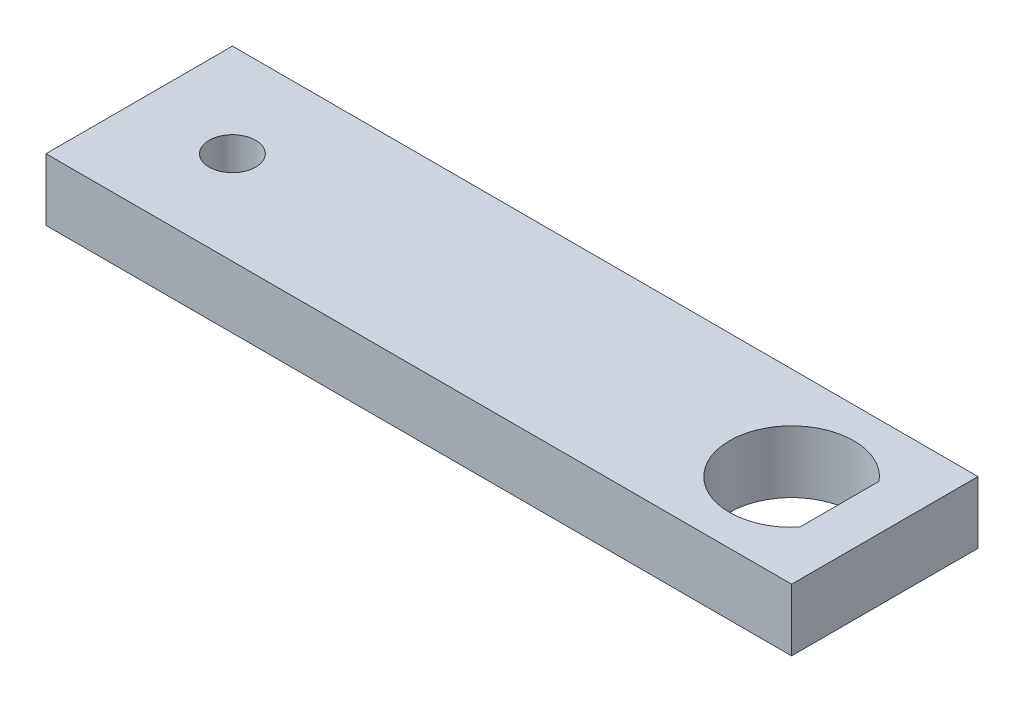
SolidWorks part; units mm, degrees
ref_plane "Front" through (0, 0, 0) normal (0, 0, 1) x (1, 0, 0)
ref_plane "Top" through (0, 0, 0) normal (0, 1, 0) x (-1, 0, 0)
ref_plane "Right" through (0, 0, 0) normal (1, 0, 0) x (0, 0, -1)
sketch "Sketch1" plane through (0, 0, 0) normal (0, 0, 1) x (1, 0, 0)
  line L0 (0, 0) -> (76.2, 0)
  line L1 (0, 0) -> (0, 6.35)
  line L2 (76.2, 6.35) -> (0, 6.35)
  line L3 (76.2, 6.35) -> (76.2, 0)
  dimension "D1" = 6.35
  dimension "D2" = 76.2
extrude "Base-Extrude" add sketch "Sketch1" along normal blind 19.05
sketch "Sketch2" plane through (0, 6.35, 0) normal (0, 1, 0) x (-1, 0, 0)
  line L0 (-76.2, 19.05) -> (-76.2, 0) construction
  line L1 (-76.2, 19.05) -> (0, 19.05) construction
  line L2 (-71.5645, 5.4734) -> (-71.5645, 13.5766)
  arc A0 (-71.5645, 5.4734) -> (-71.5645, 13.5766) centre (-66.675, 9.525) ccw
  dimension "D1" = 12.7
  dimension "D2" = 9.525
  dimension "D3" = 9.525
  dimension "D4" = 4.8895
extrude "Cut-Extrude1" cut sketch "Sketch2" against normal through all
sketch "Sketch3" plane through (0, 6.35, 0) normal (0, 1, 0) x (-1, 0, 0)
  line L0 (0, 19.05) -> (0, 0) construction
  circle A0 centre (-9.525, 9.525) radius 2.3813
  arc A1 (-71.5645, 5.4734) -> (-71.5645, 13.5766) centre (-66.675, 9.525) ccw construction
  point P5 (-66.675, 9.525)
  dimension "D1" = 4.7625
  dimension "D2" = 9.525
extrude "Cut-Extrude2" cut sketch "Sketch3" against normal through all
